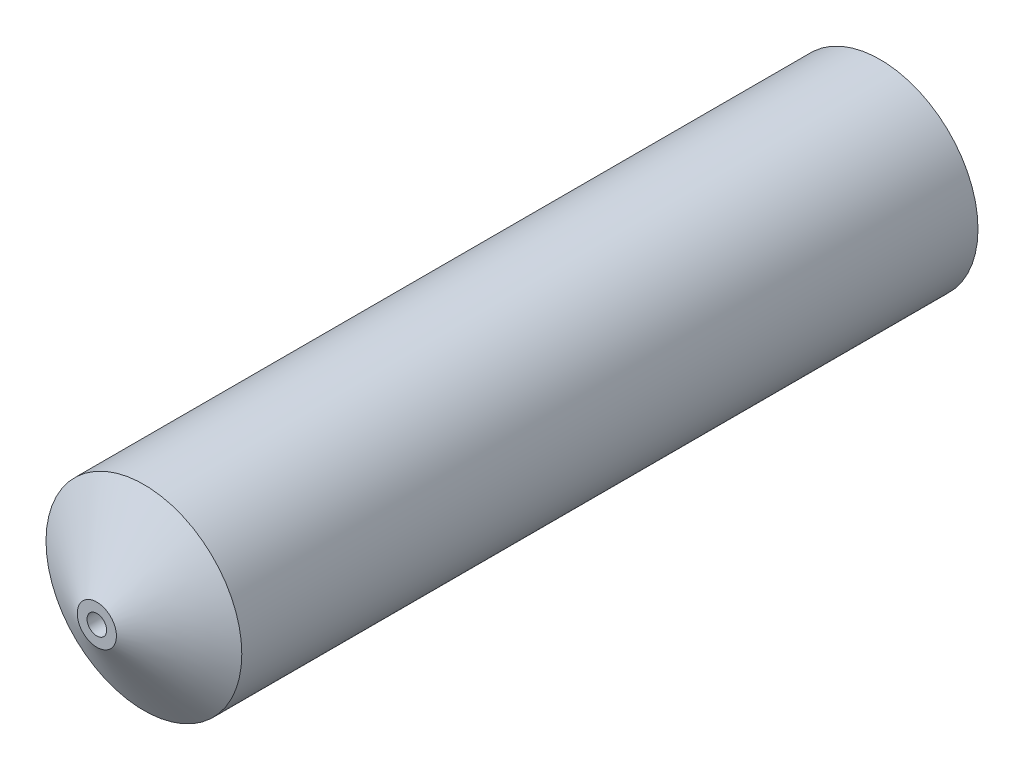
SolidWorks part; units mm, degrees
ref_plane "Front Plane" through (0, 0, 0) normal (0, 0, 1) x (1, 0, 0)
ref_plane "Top Plane" through (0, 0, 0) normal (0, 1, 0) x (1, 0, 0)
ref_plane "Right Plane" through (0, 0, 0) normal (1, 0, 0) x (0, 0, -1)
sketch "Sketch1" plane through (0, 0, 0) normal (0, 1, 0) x (1, 0, 0)
  line L0 (0, 0) -> (0, -20.6739) construction
  line L1 (0.25, -20) -> (0.5, -20)
  line L2 (0.5, -20) -> (2.5, -18.7983)
  line L7 (1.65, 0) -> (1.65, -4)
  line L9 (2.5, -18.7983) -> (2.5, 0)
  line L10 (2.5, 0) -> (1.65, 0)
  line L11 (1.65, -4) -> (1, -4)
  line L12 (1, -4) -> (1, -18.9494)
  line L13 (1, -18.9494) -> (0.25, -19.4)
  line L14 (0.25, -19.4) -> (0.25, -20)
  dimension "D1" = 5
  dimension "D2" = 3.3
  dimension "D3" = 2
  dimension "D4" = 0.5
  dimension "D5" = 1
  dimension "D6" = 20
  dimension "D7" = 4
  dimension "D11" = 59
  dimension "D12" = 0.6
revolve "Revolve1" add sketch "Sketch1" angle 360 about L0
